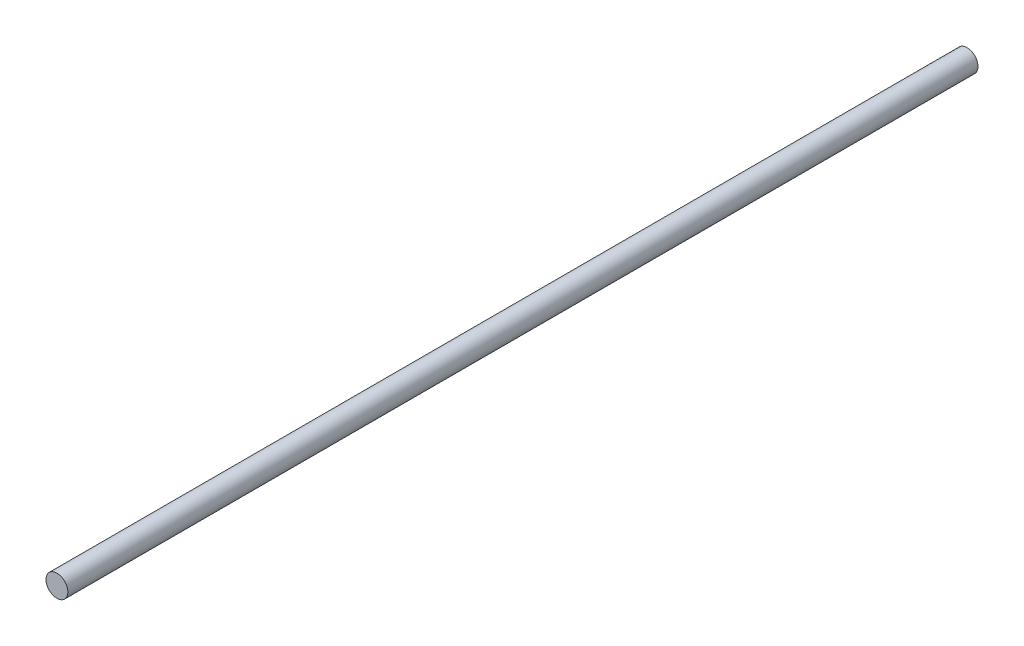
SolidWorks part; units mm, degrees
material "Hexcel AS4C (3000 Filaments)"
ref_plane "Front Plane" through (0, 0, 0) normal (0, 0, 1) x (1, 0, 0)
ref_plane "Top Plane" through (0, 0, 0) normal (0, 1, 0) x (1, 0, 0)
ref_plane "Right Plane" through (0, 0, 0) normal (1, 0, 0) x (0, 0, -1)
sketch "Sketch1" plane through (0, 0, 0) normal (0, 0, 1) x (1, 0, 0)
  circle A0 centre (0, 0) radius 3
  dimension "D1" = 6
extrude "Boss-Extrude1" add sketch "Sketch1" along normal mid plane 250
